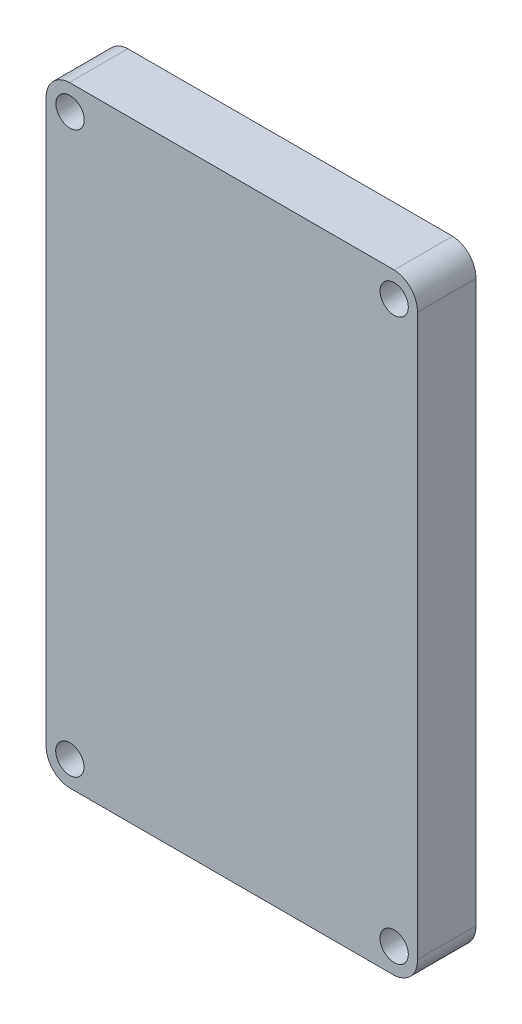
SolidWorks part; units mm, degrees
ref_plane "前视基准面" through (0, 0, 0) normal (0, 0, 1) x (1, 0, 0)
ref_plane "上视基准面" through (0, 0, 0) normal (0, 1, 0) x (1, 0, 0)
ref_plane "右视基准面" through (0, 0, 0) normal (1, 0, 0) x (0, 0, -1)
other "Configuration Table"
sketch "草图1" plane through (0, 0, 0) normal (0, 0, 1) x (1, 0, 0)
  line L8 (0, 2.75) -> (0, 64.13)
  line L9 (-2.54, 66.88) -> (-38.1, 66.88)
  line L10 (-40.64, 64.13) -> (-40.64, 2.75)
  line L11 (-38.1, 0) -> (-2.54, 0)
  circle A2 centre (-2.54, 2.75) radius 1.55
  circle A4 centre (-2.54, 64.13) radius 1.55
  circle A6 centre (-38.049, 2.75) radius 1.55
  circle A8 centre (-38.024, 64.13) radius 1.55
  arc A16 (0, 64.13) -> (-2.54, 66.88) centre (-2.6442, 64.2357) ccw
  arc A17 (-38.1, 66.88) -> (-40.64, 64.13) centre (-37.9958, 64.2357) ccw
  arc A18 (-40.64, 2.75) -> (-38.1, 0) centre (-37.9958, 2.6443) ccw
  arc A19 (-2.54, 0) -> (0, 2.75) centre (-2.6442, 2.6443) ccw
extrude "凸台-拉伸1" add sketch "草图1" along normal blind 6.4
